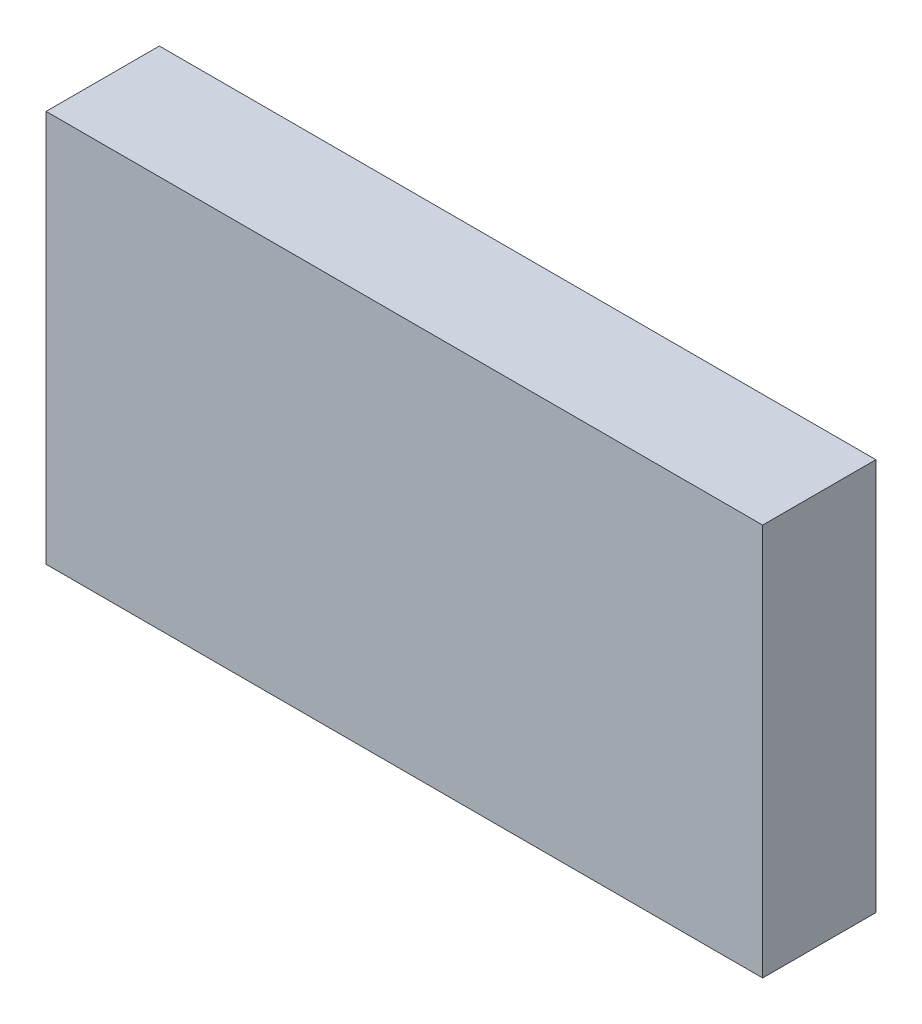
SolidWorks part; units mm, degrees
ref_plane "Front Plane" through (0, 0, 0) normal (0, 0, 1) x (1, 0, 0)
ref_plane "Top Plane" through (0, 0, 0) normal (0, 1, 0) x (1, 0, 0)
ref_plane "Right Plane" through (0, 0, 0) normal (1, 0, 0) x (0, 0, -1)
sketch "Sketch1" plane through (0, 0, 0) normal (0, 0, 1) x (1, 0, 0)
  line L0 (-3.1635, 1.7635) -> (3.1635, 1.7635)
  line L1 (3.1635, 1.7635) -> (3.1635, -1.7)
  line L2 (3.1635, -1.7) -> (-3.1635, -1.7)
  line L3 (-3.1635, -1.7) -> (-3.1635, 1.7635)
extrude "Component_Outline" add sketch "Sketch1" along normal blind 1 separate body
sketch3d "3DSketch1"
  line L0 (0, 0, 0) -> (1, 0, 0)
  line L1 (0, 0, 0) -> (0, 1, 0)
  line L2 (0, 0, 0) -> (0, 0, 1)
  point P0 (0, 0, 0)
